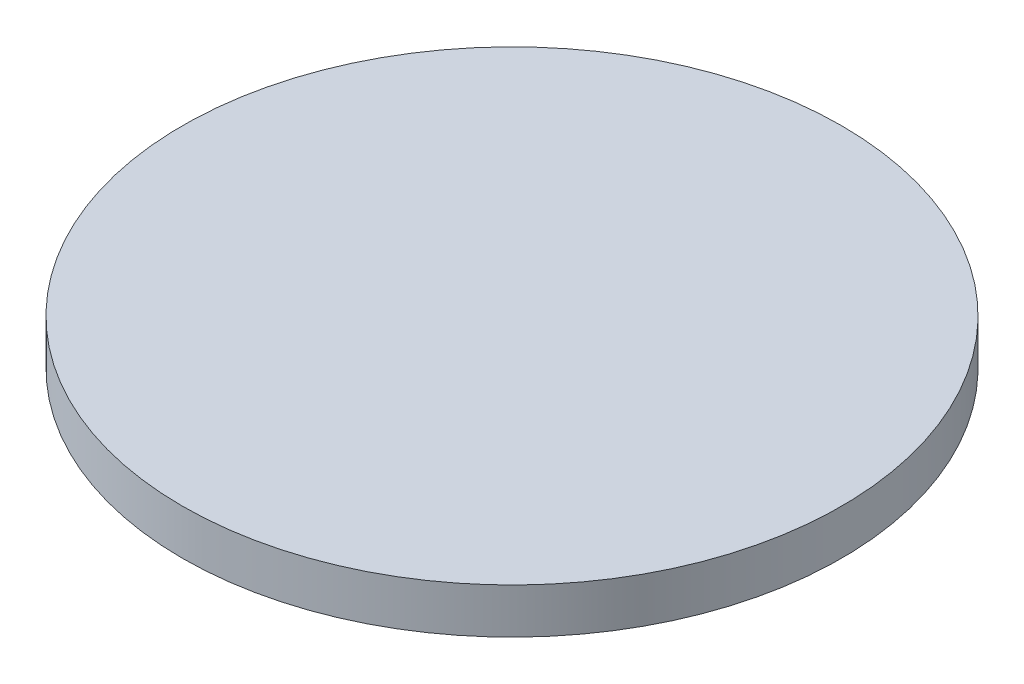
SolidWorks part; units mm, degrees
ref_plane "Front Plane" through (0, 0, 0) normal (0, 0, 1) x (1, 0, 0)
ref_plane "Top Plane" through (0, 0, 0) normal (0, 1, 0) x (1, 0, 0)
ref_plane "Right Plane" through (0, 0, 0) normal (1, 0, 0) x (0, 0, -1)
sketch "Sketch1" plane through (0, 0, 0) normal (0, 1, 0) x (1, 0, 0)
  circle A0 centre (0, 0) radius 72.95
  dimension "D1" = 145.9
extrude "Boss-Extrude1" add sketch "Sketch1" along normal blind 10 contours A0
